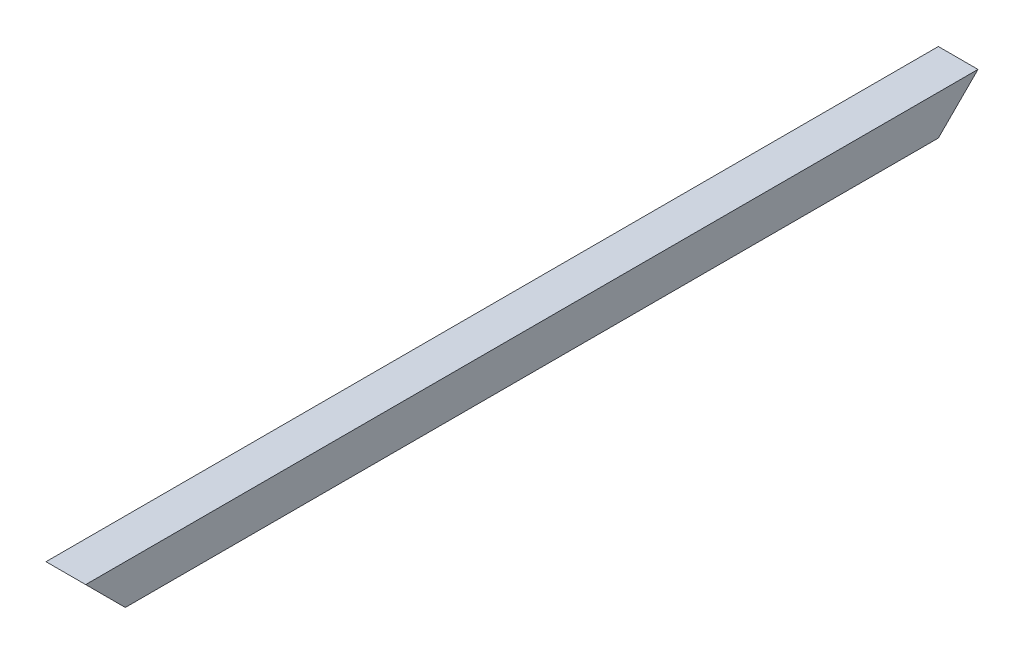
SolidWorks part; units mm, degrees
material "Plain Carbon Steel"
ref_plane "Front Plane" through (0, 0, 0) normal (0, 0, 1) x (1, 0, 0)
ref_plane "Top Plane" through (0, 0, 0) normal (0, 1, 0) x (1, 0, 0)
ref_plane "Right Plane" through (0, 0, 0) normal (1, 0, 0) x (0, 0, -1)
sketch "Sketch1" plane through (0, 0, 0) normal (0, 0, 1) x (1, 0, 0)
  line B0 (-50, -50) -> (50, -50)
  line B1 (-50, -50) -> (-50, 50)
  line B2 (50, -50) -> (50, 50)
  line B3 (-50, 50) -> (50, 50)
  line B4 (-45, -45) -> (45, -45)
  line B5 (-45, -45) -> (-45, 45)
  line B6 (45, -45) -> (45, 45)
  line B7 (-45, 45) -> (45, 45)
sketch_block_instance "10x10x5_profil-1"
sketch_block "10x10x5_profil" parameters "D1"=100, "D2"=100, "D3"=5, "D4"=5
extrude "Boss-Extrude1" add sketch "Sketch1" along normal mid plane 2250
sketch "Sketch4" plane through (0, 0, 0) normal (1, 0, 0) x (0, 0, -1)
  line L0 (-1125, 50) -> (-1025, -50)
  line L1 (-1125, -50) -> (1125, -50) construction
  line L2 (1125, 50) -> (1025, -50)
  line L3 (-1125, 50) -> (1125, 50) construction
  line L4 (-1125, 50) -> (-1125, -50)
  line L5 (-1125, -50) -> (-1025, -50)
  line L6 (1025, -50) -> (1125, -50)
  line L7 (1125, -50) -> (1125, 50)
  dimension "D1" = 45
  dimension "D2" = 45
extrude "Cut-Extrude1" cut sketch "Sketch4" along normal through all and the other way through all
